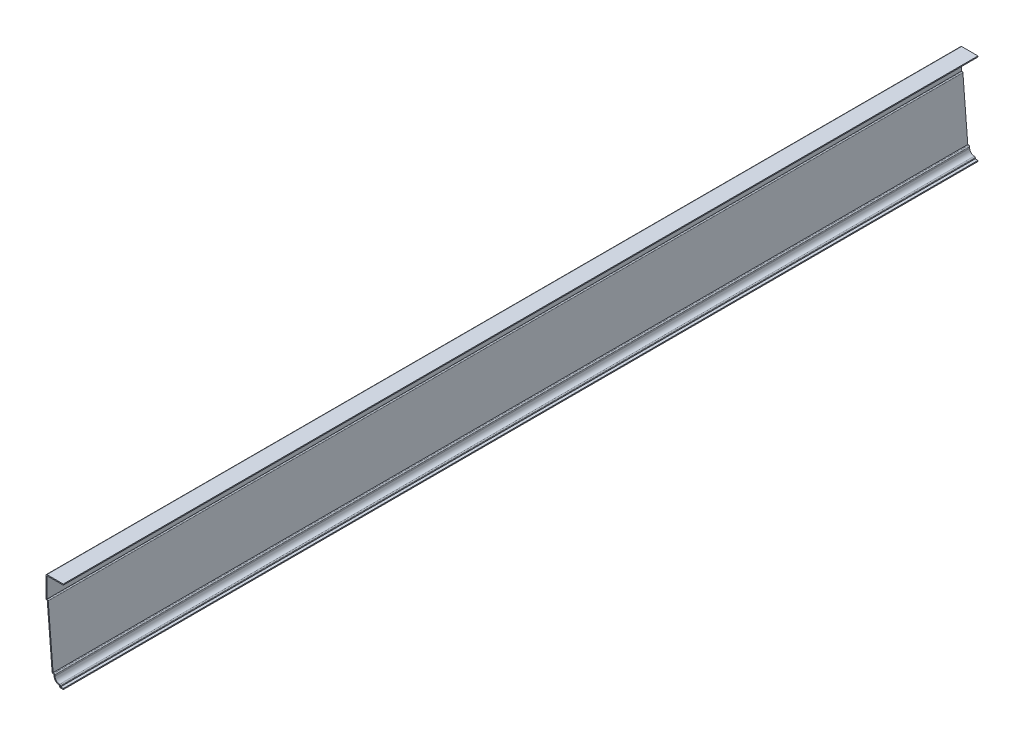
SolidWorks part; units mm, degrees
ref_plane "Front Plane" through (0, 0, 0) normal (0, 0, 1) x (1, 0, 0)
ref_plane "Top Plane" through (0, 0, 0) normal (0, 1, 0) x (1, 0, 0)
ref_plane "Right Plane" through (0, 0, 0) normal (1, 0, 0) x (0, 0, -1)
sketch "Sketch1" plane through (0, 0, 0) normal (0, 0, 1) x (1, 0, 0)
  line L0 (0, 0) -> (0, 117.475) construction
  line L1 (0, 0) -> (-4.7625, 0)
  line L2 (-4.7625, 0) -> (-4.7625, 2.3812)
  line L3 (-11.9062, 9.525) -> (-11.9062, 11.1125)
  line L4 (-11.9062, 11.1125) -> (-14.2875, 11.1125)
  line L5 (-14.2875, 11.1125) -> (-20.6375, 88.9)
  line L6 (-20.6375, 88.9) -> (-22.225, 88.9)
  line L7 (-22.225, 88.9) -> (-22.225, 117.475)
  line L8 (-22.225, 117.475) -> (0, 117.475)
  arc A0 (-4.7625, 2.3812) -> (-11.9062, 9.525) centre (-4.7625, 9.525) cw
  point P7 (0, 0)
  point P13 (-4.7625, 2.4531)
  point P14 (0, 0)
  dimension "D1" = 117.475
  dimension "D2" = 4.7625
  dimension "D3" = 7.1437
  dimension "D4" = 2.3813
  dimension "D5" = 6.35
  dimension "D6" = 1.5875
  dimension "D7" = 22.225
  dimension "D8" = 28.575
  dimension "D9" = 77.7875
  dimension "D10" = 8.7312
  dimension "D11" = 2.3812
extrude "Extrude-Thin1" add sketch "Sketch1" against normal blind 1174.75 thin
fillet "Fillet1" radius 1.27 7 edges at (-4.7625, 0, -587.375) (-3.4925, 3.7902, -587.375) (-10.6363, 12.3825, -587.375) (-14.2875, 11.1125, -587.375) (-22.225, 88.9, -587.375) (-19.4669, 90.17, -587.375) (-22.225, 117.475, -587.375)
